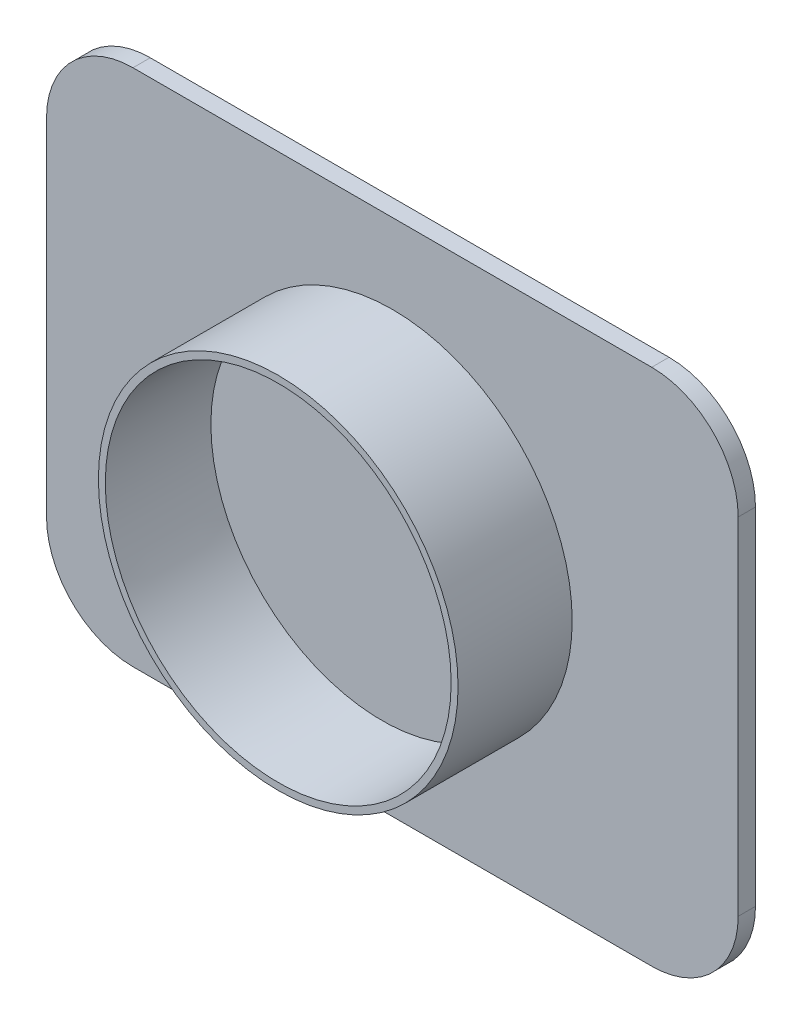
SolidWorks part; units mm, degrees
ref_plane "Plan de face" through (0, 0, 0) normal (0, 0, 1) x (1, 0, 0)
ref_plane "Plan de dessus" through (0, 0, 0) normal (0, 1, 0) x (1, 0, 0)
ref_plane "Plan de droite" through (0, 0, 0) normal (1, 0, 0) x (0, 0, -1)
sketch "Esquisse1" plane through (0, 0, 0) normal (0, 0, 1) x (1, 0, 0)
  circle A0 centre (0, 0) radius 10.4
  dimension "D1" = 20.8
extrude "Boss.-Extru.1" add sketch "Esquisse1" along normal blind 6.6
sketch "Esquisse2" plane through (0, 0, 6.6) normal (0, 0, 1) x (1, 0, 0)
  circle A0 centre (0, 0) radius 10
  dimension "D1" = 20
extrude "Enlèv. mat.-Extru.1" cut sketch "Esquisse2" against normal blind 6 draft 1
sketch "Esquisse3" plane through (0, 0, 0) normal (0, 0, 1) x (1, 0, 0)
  line L1 (20, 15) -> (-20, 15)
  line L2 (20, 15) -> (20, -15)
  line L3 (20, -15) -> (-20, -15)
  line L4 (-20, 15) -> (-20, -15)
  line L5 (20, 15) -> (-20, -15) construction
  line L6 (20, -15) -> (-20, 15) construction
  point P0 (0, 0)
  point P6 (-21.7419, 18.2632)
  dimension "D1" = 40
  dimension "D2" = 30
extrude "Boss.-Extru.2" add sketch "Esquisse3" against normal blind 1
fillet "Congé1" radius 5 4 edges at (20, 15, -0.5) (20, -15, -0.5) (-20, -15, -0.5) (-20, 15, -0.5)
